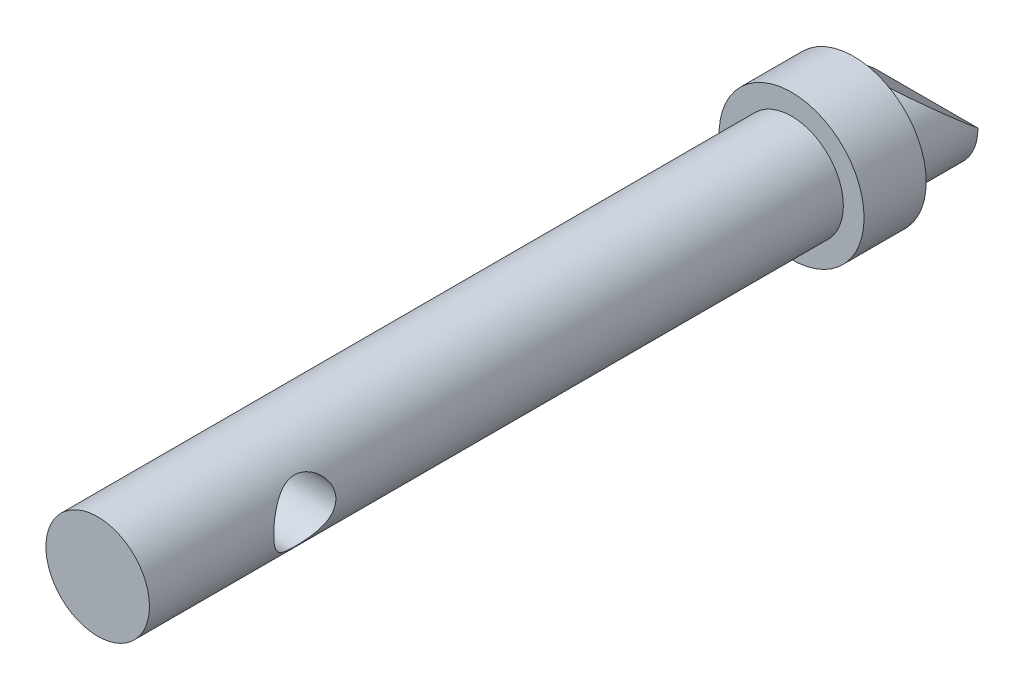
SolidWorks part; units mm, degrees
ref_plane "Front Plane" through (0, 0, 0) normal (0, 0, 1) x (1, 0, 0)
ref_plane "Top Plane" through (0, 0, 0) normal (0, 1, 0) x (1, 0, 0)
ref_plane "Right Plane" through (0, 0, 0) normal (1, 0, 0) x (0, 0, -1)
sketch "Sketch1" plane through (0, 0, 0) normal (0, 0, 1) x (1, 0, 0)
  circle A0 centre (0, 0) radius 2.5
  dimension "D1" = 5
extrude "Boss-Extrude1" add sketch "Sketch1" along normal blind 35 and the other way blind 5
sketch "Sketch2" plane through (0, 0, 0) normal (0, 0, 1) x (1, 0, 0)
  circle A0 centre (0, 0) radius 3.5
  dimension "D1" = 7
extrude "Boss-Extrude2" add sketch "Sketch2" along normal blind 1.5 and the other way blind 1.5
sketch "Sketch3" plane through (0, 0, 0) normal (1, 0, 0) x (0, 0, -1)
  line L0 (-27.5, 0) -> (0, 0) construction
  circle A0 centre (-27.5, 0) radius 1.5
  dimension "D1" = 3
  dimension "D2" = 27.5
extrude "Cut-Extrude1" cut sketch "Sketch3" along normal through all both and the other way through all
sketch "Sketch4" plane through (0, 0, 0) normal (1, 0, 0) x (0, 0, -1)
  line L0 (5, 0) -> (2, 2.5)
  line L1 (5, -2.5) -> (5, 2.5) construction
  line L2 (5, 2.5) -> (1.5, 2.5) construction
  line L3 (2, 2.5) -> (5, 2.5)
  line L4 (5, 2.5) -> (5, 0)
  dimension "D1" = 3
extrude "Cut-Extrude2" cut sketch "Sketch4" against normal through all both and the other way through all
